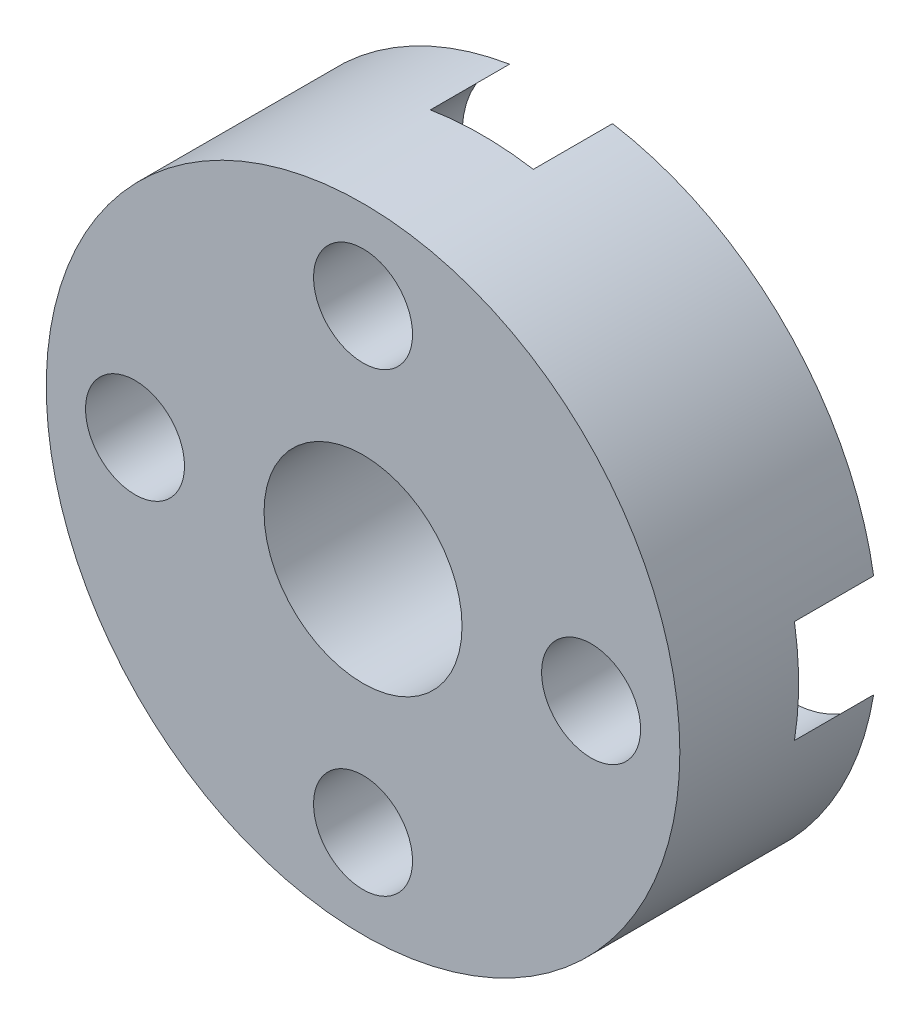
SolidWorks part; units mm, degrees
material "ABS"
ref_plane "前视基准面" through (0, 0, 0) normal (0, 0, 1) x (1, 0, 0)
ref_plane "上视基准面" through (0, 0, 0) normal (0, 1, 0) x (1, 0, 0)
ref_plane "右视基准面" through (0, 0, 0) normal (1, 0, 0) x (0, 0, -1)
other "Configuration Table"
sketch "草图1" plane through (0, 0, 0) normal (0, 0, 1) x (1, 0, 0)
  circle A0 centre (-420.4541, 61.6664) radius 8
  circle A1 centre (-420.4541, 61.6664) radius 5.7583 construction
  circle A2 centre (-420.4541, 61.6664) radius 2.5
  circle A3 centre (-420.4541, 67.4246) radius 1.25
  circle A4 centre (-414.6959, 61.6664) radius 1.25
  circle A5 centre (-420.4541, 55.9081) radius 1.25
  circle A6 centre (-426.2124, 61.6664) radius 1.25
  dimension "D1" = 16
  dimension "D2" = 5
  dimension "D3" = 2.5
extrude "凸台-拉伸1" add sketch "草图1" along normal blind 5
sketch "草图2" plane through (0, 0, 0) normal (0, 0, -1) x (-1, 0, 0)
  circle A0 centre (420.4541, 67.4246) radius 2.5
  circle A1 centre (426.2124, 61.6664) radius 2.5
  circle A2 centre (420.4541, 55.9081) radius 2.5
  circle A3 centre (414.6959, 61.6664) radius 2.5
  circle A4 centre (414.6959, 61.6664) radius 1.25 construction
  circle A5 centre (426.2124, 61.6664) radius 1.25 construction
  circle A6 centre (420.4541, 55.9081) radius 1.25 construction
  circle A7 centre (420.4541, 67.4246) radius 1.25 construction
  dimension "D1" = 5
extrude "切除-拉伸1" cut sketch "草图2" against normal blind 2
